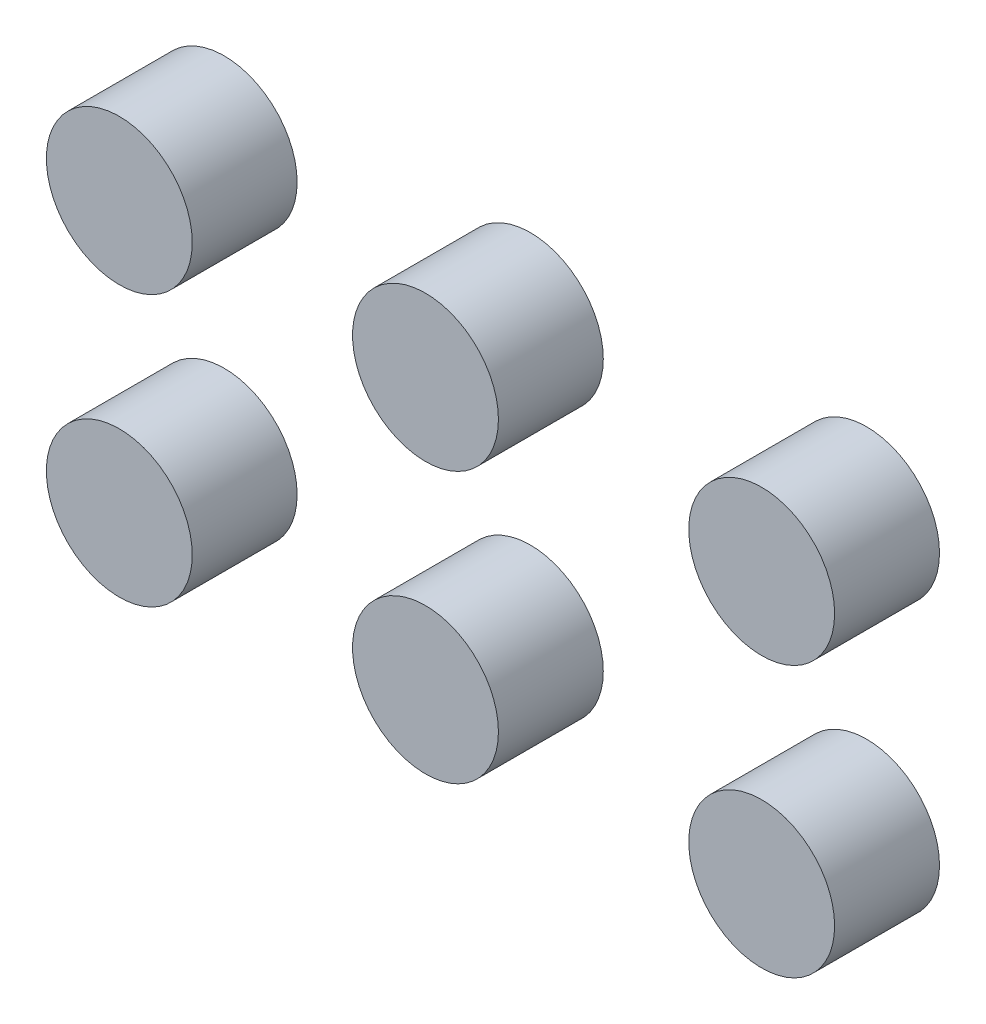
SolidWorks part; units mm, degrees
other "Body6"
other "Body5"
other "Body4"
other "Body3"
other "Body2"
other "Body1"
ref_plane "Front Plane" through (0, 0, 0) normal (0, 0, 1) x (1, 0, 0)
ref_plane "Top Plane" through (0, 0, 0) normal (0, 1, 0) x (1, 0, 0)
ref_plane "Right Plane" through (0, 0, 0) normal (1, 0, 0) x (0, 0, -1)
sketch "Sketch1" plane through (0, 0, 0) normal (0, 0, 1) x (1, 0, 0)
  circle A0 centre (-136.7704, 40.2984) radius 27.8175
  circle A1 centre (-19.9966, 40.2984) radius 27.8175
  circle A2 centre (108.2257, 40.2984) radius 27.8175
  circle A3 centre (-136.7704, -62.89) radius 27.8175
  circle A4 centre (-19.9966, -62.89) radius 27.8175
  circle A5 centre (108.2257, -62.89) radius 27.8175
extrude "Boss-Extrude1" add sketch "Sketch1" along normal blind 40
equation "\"Var1\"= 1::swApp.RunAttachedMacro \"rename bodies.swp\", \"mMain\", \"main\""
